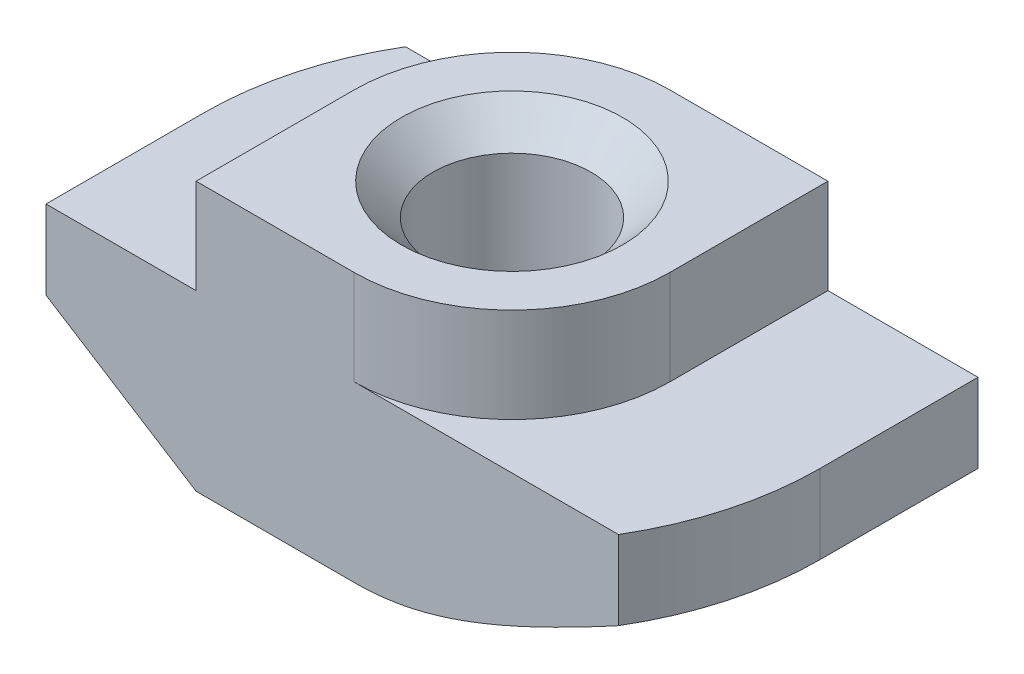
SolidWorks part; units mm, degrees
material "Сталь 20  ГОСТ 1050-2013"
ref_plane "Спереди" through (0, 0, 0) normal (0, 0, 1) x (1, 0, 0)
ref_plane "Сверху" through (0, 0, 0) normal (0, 1, 0) x (1, 0, 0)
ref_plane "Справа" through (0, 0, 0) normal (1, 0, 0) x (0, 0, -1)
sketch "Эскиз1" plane through (0, 0, 0) normal (0, 0, 1) x (1, 0, 0)
  line L0 (5, 0) -> (-5, 0)
  line L1 (-5, 0) -> (-5, -3)
  line L2 (-5, -3) -> (-9.75, -3)
  line L3 (-9.75, -3) -> (-9.75, -8.5)
  line L4 (-9.75, -8.5) -> (9.75, -8.5)
  line L5 (0, -8.5) -> (0, 0) construction
  line L6 (9.75, -3) -> (9.75, -8.5)
  line L7 (5, -3) -> (9.75, -3)
  line L8 (5, 0) -> (5, -3)
  dimension "D1" = 10
  dimension "D2" = 19.5
  dimension "D3" = 8.5
  dimension "D4" = 3
extrude "Бобышка-Вытянуть1" add sketch "Эскиз1" along normal mid plane 10
hole_wizard "Отверстие обработанное метчиком M62" positions "Эскиз2" profile "Эскиз3" tap size "M6" standard "ISO" end condition up to next
sketch "Эскиз2" plane through (0, 0, 0) normal (0, 1, 0) x (1, 0, 0)
  point P0 (0, 0)
sketch "Эскиз3" plane through (0, 0, 0) normal (1, 0, 0) x (0, 0, 1)
  line L0 (0, 0) -> (0, 8.5)
  line L1 (0, 8.5) -> (3.5, 8.5)
  line L2 (2.5, 7.5) -> (2.5, 1)
  line L3 (2.5, 1) -> (3.5, 0)
  line L5 (3.5, 0) -> (0, 0)
  line L6 (-2.5, 1) -> (-3.5, 0) construction
  line L7 (3.5, 8.5) -> (2.5, 7.5)
  line L8 (-3.5, 8.5) -> (-2.5, 7.5) construction
  line L11 (0, -6.35) -> (0, 107.95) construction
  dimension "Диаметр проходного сверла" = 5
  dimension "Глубина проходного сверла" = 8.5
  dimension "Диаметр передней зенковки" = 7
  dimension "Угол передней зенковки" = 90
  dimension "Диаметр задней зенковки" = 7
  dimension "Угол задней зенковки" = 90
cosmetic thread "Отверстие резьбы1" parameters "D2"=6
sketch "Эскиз4" plane through (0, 0, 0) normal (0, 1, 0) x (1, 0, 0)
  line L0 (-5, 5) -> (-5, 0)
  line L1 (-5, -5) -> (-5, 5) construction
  line L2 (5, 5) -> (-5, 5) construction
  line L3 (0, 5) -> (-5, 5)
  line L4 (0, -5) -> (5, -5)
  line L5 (5, -5) -> (-5, -5) construction
  line L6 (5, -5) -> (5, 0)
  line L7 (5, -5) -> (5, 5) construction
  arc A0 (-5, 0) -> (0, 5) centre (0, 0) cw
  arc A1 (5, 0) -> (0, -5) centre (0, 0) cw
extrude "Вырез-Вытянуть1" cut sketch "Эскиз4" against normal up to surface (3 mm away) up to face at (-7.375, -3, 0)
sketch "Эскиз5" plane through (0, -3, 0) normal (0, 1, 0) x (1, 0, 0)
  line L0 (-9.75, 0) -> (-9.75, 5)
  line L1 (-9.75, -5) -> (-9.75, 5) construction
  line L2 (-9.75, 5) -> (-8.3703, 5)
  line L3 (0, 5) -> (-9.75, 5) construction
  line L4 (9.75, 0) -> (9.75, -5)
  line L5 (9.75, -5) -> (9.75, 5) construction
  line L6 (9.75, -5) -> (8.3703, -5)
  line L7 (9.75, -5) -> (0, -5) construction
  arc A0 (-8.3703, 5) -> (-9.75, 0) centre (0, 0) ccw
  arc A2 (9.75, 0) -> (8.3703, -5) centre (0, 0) cw
  point P19 (0, 0)
extrude "Вырез-Вытянуть2" cut sketch "Эскиз5" against normal through all
sketch "Эскиз6" plane through (0, 0, 5) normal (0, 0, 1) x (1, 0, 0)
  line L0 (-9.75, -5.5) -> (-9.75, -8.5)
  line L1 (-9.75, -3) -> (-9.75, -8.5) construction
  line L2 (-9.75, -8.5) -> (-5, -8.5)
  line L3 (-9.75, -8.5) -> (8.3703, -8.5) construction
  line L4 (-5, -8.5) -> (-9.75, -5.5)
  line L5 (-5, -3) -> (-9.75, -3) construction
  line L6 (-5, 0) -> (-5, -3) construction
  point P10 (0, 0)
  dimension "D1" = 2.5
sketch "Эскиз7" plane through (0, -8.5, 0) normal (0, -1, 0) x (1, 0, 0)
  line L0 (0, 9.75) -> (-9.75, 9.75)
  line L1 (-9.75, 9.75) -> (-9.75, 0)
  line L2 (0, -9.75) -> (9.75, -9.75)
  line L3 (9.75, -9.75) -> (9.75, 0)
  arc A0 (-9.75, 0) -> (0, -9.75) centre (0, 0) ccw
  arc A1 (9.75, 0) -> (0, 9.75) centre (0, 0) ccw
sweep "Вырез-По траектории1" cut profiles "Эскиз6" path "Эскиз7"
